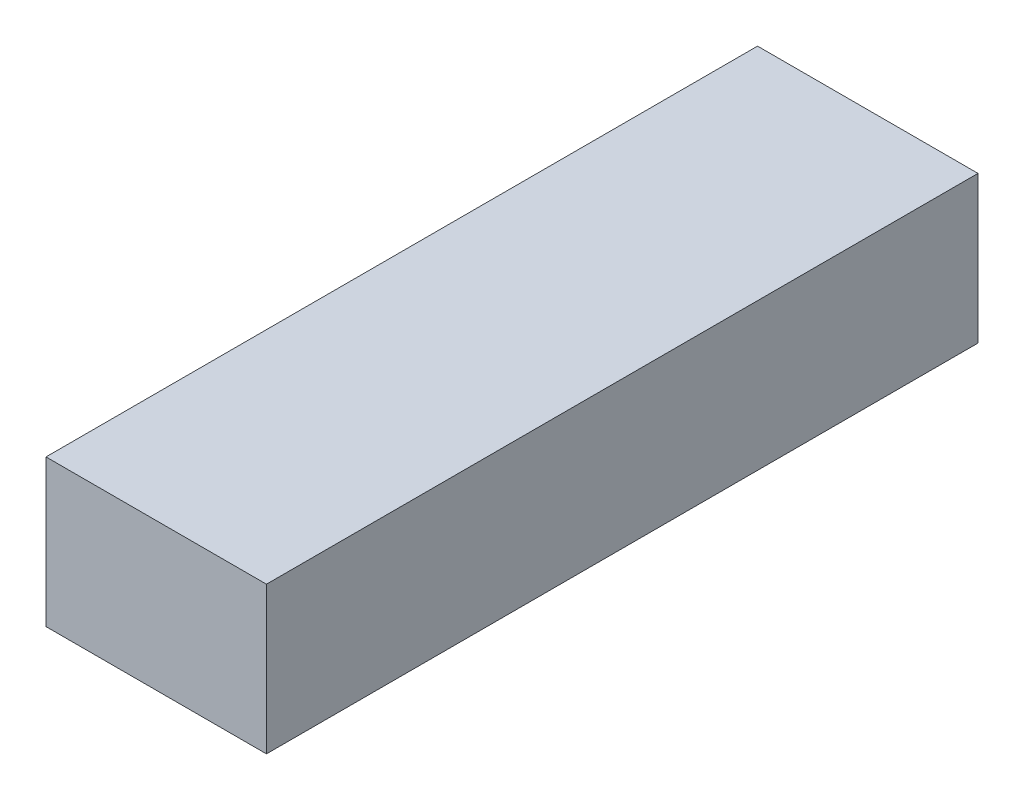
SolidWorks part; units mm, degrees
ref_plane "Front Plane" through (0, 0, 0) normal (0, 0, 1) x (1, 0, 0)
ref_plane "Top Plane" through (0, 0, 0) normal (0, 1, 0) x (1, 0, 0)
ref_plane "Right Plane" through (0, 0, 0) normal (1, 0, 0) x (0, 0, -1)
sketch "Sketch1" plane through (0, 0, 0) normal (0, 0, 1) x (1, 0, 0)
  line L1 (24.003, 16.002) -> (-24.003, 16.002)
  line L2 (24.003, 16.002) -> (24.003, -16.002)
  line L3 (24.003, -16.002) -> (-24.003, -16.002)
  line L4 (-24.003, 16.002) -> (-24.003, -16.002)
  line L5 (24.003, 16.002) -> (-24.003, -16.002) construction
  line L6 (24.003, -16.002) -> (-24.003, 16.002) construction
  point P0 (0, 0)
  dimension "D1" = 48.006
  dimension "D2" = 32.004
extrude "Boss-Extrude1" add sketch "Sketch1" along normal blind 154.94
